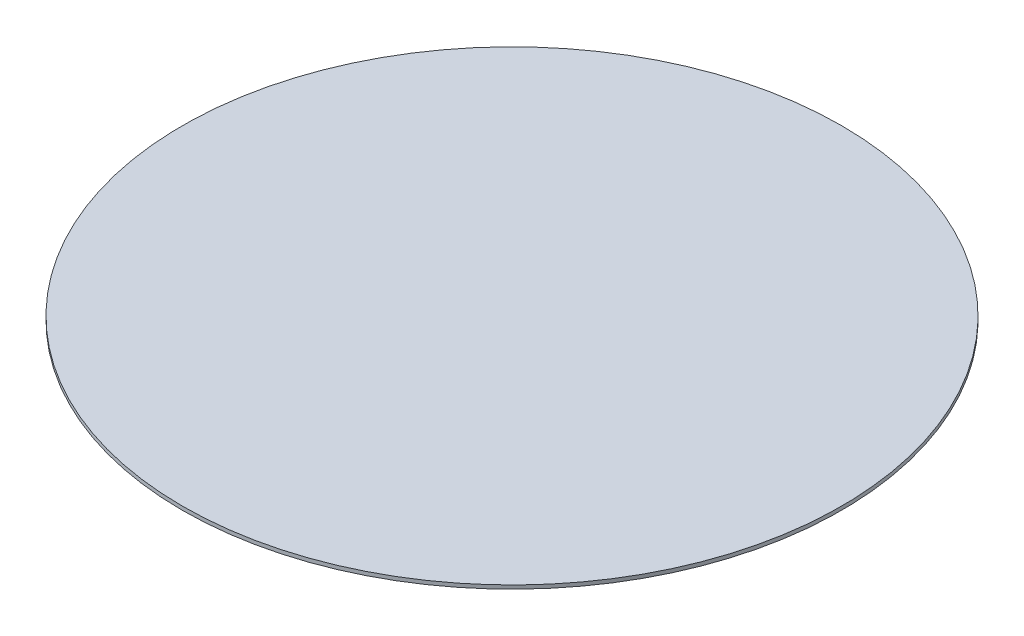
SolidWorks part; units mm, degrees
ref_plane "Front Plane" through (0, 0, 0) normal (0, 0, 1) x (1, 0, 0)
ref_plane "Top Plane" through (0, 0, 0) normal (0, 1, 0) x (1, 0, 0)
ref_plane "Right Plane" through (0, 0, 0) normal (1, 0, 0) x (0, 0, -1)
sketch "Sketch1" plane through (0, 0, 0) normal (0, 1, 0) x (1, 0, 0)
  circle A0 centre (0, 0) radius 90
  dimension "D1" = 180
extrude "Boss-Extrude1" add sketch "Sketch1" along normal blind 1
